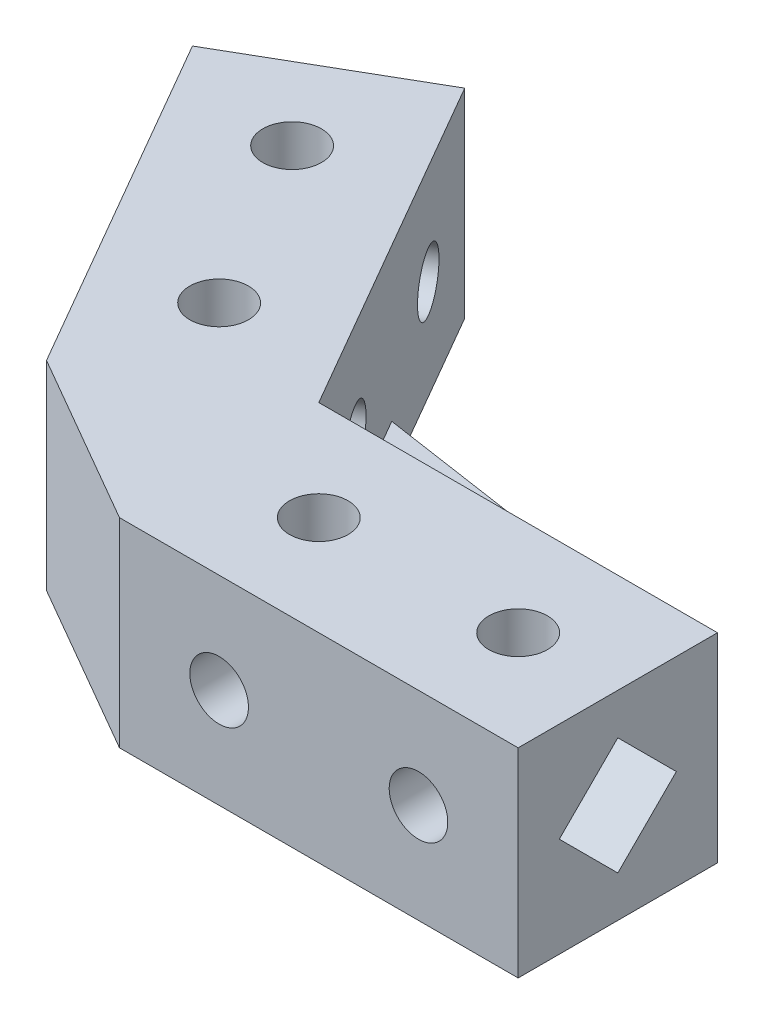
SolidWorks part; units mm, degrees
ref_plane "Front Plane" through (0, 0, 0) normal (0, 0, 1) x (1, 0, 0)
ref_plane "Top Plane" through (0, 0, 0) normal (0, 1, 0) x (1, 0, 0)
ref_plane "Right Plane" through (0, 0, 0) normal (1, 0, 0) x (0, 0, -1)
other "Configuration Table"
sketch "sketch1" plane through (0, 0, 0) normal (0, 1, 0) x (1, 0, 0)
  line L0 (0, -8.5) -> (8.5, -8.5) construction
  line L1 (0, 0) -> (34, 0)
  line L2 (0, 0) -> (0, -17)
  line L3 (0, -17) -> (34, -17)
  line L4 (34, 0) -> (34, -17)
  line L5 (8.5, -8.5) -> (25.5, -8.5) construction
  circle A1 centre (8.5, -8.5) radius 2.5
  circle A2 centre (25.5, -8.5) radius 2.5
  dimension "D4" = 5
  dimension "D1" = 17
  dimension "D2" = 34
  dimension "D3" = 8.5
  dimension "D6" = 17
  dimension "D5" = 2
extrude "Boss-Extrude1" add sketch "sketch1" along normal blind 17
sketch "Sketch6" plane through (0, 0, 0) normal (0, 0, -1) x (-1, 0, 0)
  line L0 (-34, 8.5) -> (-25.5, 8.5) construction
  line L1 (-25.5, 8.5) -> (-8.5, 8.5) construction
  line L4 (-34, 0) -> (0, 0)
  line L5 (0, 0) -> (0, 17)
  line L6 (0, 17) -> (-34, 17)
  line L7 (-34, 17) -> (-34, 0)
  line L8 (-34, 0) -> (0, 0)
  line L9 (0, 0) -> (0, 17)
  line L10 (0, 17) -> (-34, 17)
  line L11 (-34, 17) -> (-34, 0)
  circle A0 centre (-25.5, 8.5) radius 2.5
  circle A1 centre (-8.5, 8.5) radius 2.5
  dimension "D3" = 5
  dimension "D2" = 8.5
  dimension "D5" = 17
  dimension "D4" = 2
extrude "Cut-Extrude10" cut sketch "Sketch6" against normal through all flip side to cut
sketch "Sketch7" plane through (34, 0, 0) normal (1, 0, 0) x (0, 0, -1)
  line L0 (-17, 8.5) -> (0, 8.5) construction
  line L1 (-8.5, 8.5) -> (-8.5, 13.4922) construction
  line L2 (-8.5, 13.4922) -> (-3.5078, 8.5)
  line L3 (-3.5078, 8.5) -> (-8.5, 3.5078)
  line L4 (-17, 0) -> (0, 0)
  line L5 (0, 0) -> (0, 17)
  line L6 (0, 17) -> (-17, 17)
  line L7 (-17, 17) -> (-17, 0)
  line L8 (-17, 0) -> (0, 0)
  line L9 (0, 0) -> (0, 17)
  line L10 (0, 17) -> (-17, 17)
  line L11 (-17, 17) -> (-17, 0)
  line L12 (-8.5, 3.5078) -> (-13.4922, 8.5)
  line L13 (-13.4922, 8.5) -> (-8.5, 13.4922)
  dimension "D2" = 7.06
extrude "Cut-Extrude11" cut sketch "Sketch7" against normal blind 17 flip side to cut
sketch "Sketch9" plane through (0, 0, 0) normal (0, 1, 0) x (1, 0, 0)
  line L0 (0, 0) -> (34, 0) construction
  line L1 (0, 0) -> (17, 29.4449) construction
  dimension "D1" = 60
ref_plane "Plane2" through (0, 0, 0) normal (-0.866, 0, -0.5) x (-0.5, 0, 0.866)
mirror "Mirror6" about plane through (0, 0, 0) normal (-0.866, 0, -0.5) of bodies 118 110
sketch "Sketch11" plane through (0, 0, 0) normal (0, 1, 0) x (1, 0, 0)
  line L0 (-14.7224, -8.5) -> (0, -17)
  line L1 (0, 0) -> (-14.7224, -8.5) construction
  line L2 (0, 0) -> (0, -17) construction
  line L3 (0, 0) -> (-14.7224, -8.5)
  line L4 (0, 0) -> (0, -17)
extrude "Boss-Extrude2" add sketch "Sketch11" along normal blind 17
sketch "Sketch13" plane through (0, 0, 0) normal (0, 1, 0) x (1, 0, 0)
  line L0 (-11.6112, 3.1112) -> (4.6528, 8.059) construction
  line L1 (0, 0) -> (17, 29.4449) construction
  line L2 (4.6528, 8.059) -> (8.5, -8.5) construction
  line L4 (7.1528, 12.3891) -> (-8.5, 14.7224)
  line L5 (-17, 29.4449) -> (0, 0) construction
  line L6 (7.1528, 12.3891) -> (17, 0)
  line L7 (0, 0) -> (34, 0) construction
  line L8 (0, 0) -> (17, 29.4449) construction
  line L9 (-8.5, 14.7224) -> (0, 0)
  line L10 (0, 0) -> (17, 0)
  circle A0 centre (8.5, -8.5) radius 2.5 construction
  circle A1 centre (-11.6112, 3.1112) radius 2.5 construction
  circle A2 centre (8.5, -8.5) radius 2.5 construction
  circle A3 centre (-11.6112, 3.1112) radius 2.5 construction
  circle A4 centre (4.6528, 8.059) radius 2.5
  dimension "D1" = 17
  dimension "D3" = 5
  dimension "D2" = 5
  dimension "D4" = 17
extrude "Boss-Extrude3" add sketch "Sketch13" along normal blind 4
equation "\"D2@sketch1\" = \"length\""
equation "\"holes\"= 2'Holes per side"
equation "\"cdist\"= 17mm'centre distance between holes"
equation "\"width\"= 17mm"
equation "\"length\"= \"cdist\" * \"holes\""
equation "\"D1@sketch1\"=\"width\""
equation "\"hdiam\"= 5mm'Hole diametre"
equation "\"D4@sketch1\" = \"hdiam\""
equation "\"D6@sketch1\" = \"cdist\""
equation "\"D5@sketch1\" = \"holes\""
equation "\"D2@Sketch6\"=\"cdist\"/2"
equation "\"D3@Sketch6\"=\"hdiam\""
equation "\"D5@Sketch6\"=\"cdist\""
equation "\"D4@Sketch6\"=\"holes\""
equation "\"D1@Boss-Extrude1\"=\"width\""
equation "\"joint\"= 120"
equation "\"D1@Sketch9\"=\"joint\"/2"
equation "\"D1@Boss-Extrude2\"=\"width\""
equation "\"D2@Sketch13\"=\"hdiam\""
equation "\"D4@Sketch13\"=\"cdist\""
equation "\"D1@Boss-Extrude3\"=\"supportheight\""
equation "\"supportheight\"= 4mm"
equation "\"tolerance\"= 0.06mm"
equation "\"insetwidth\"= 7mm"
equation "\"D2@Sketch7\"=\"insetwidth\"+\"tolerance\""
equation "\"D1@Cut-Extrude11\"=\"cdist\""
equation "\"true\"= 1"
equation "\"false\"= 0"
equation "\"centresupport\"= \"true\""
equation "\"Boss-Extrude3\"= IIF ( \"centresupport\" < \"true\" , \"suppressed\" , \"unsuppressed\" )"
